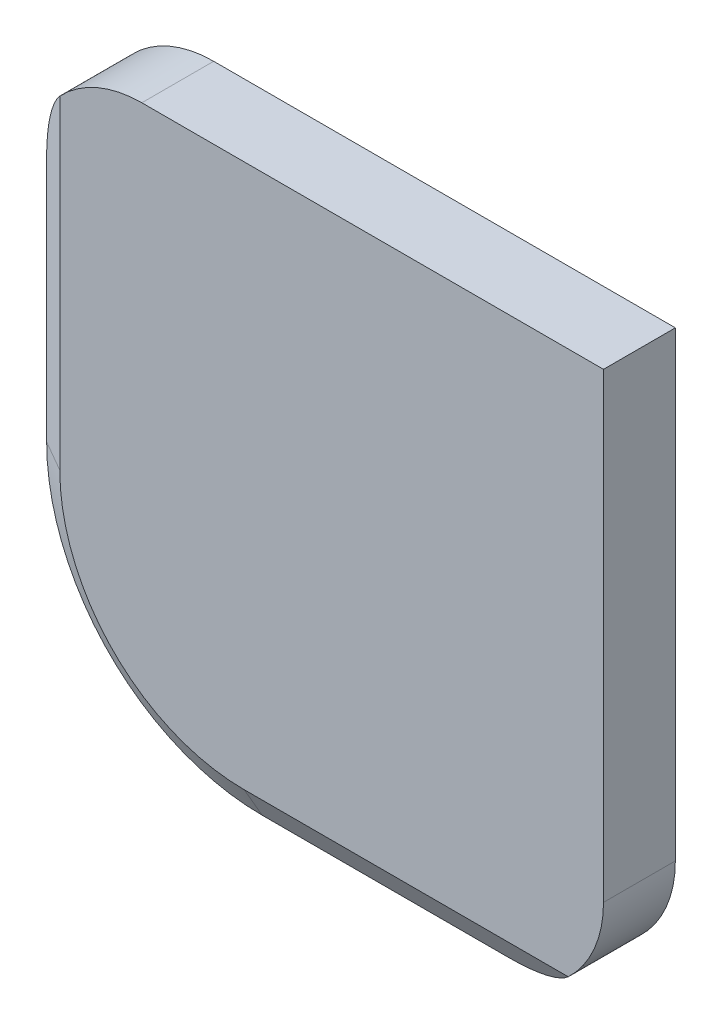
SolidWorks part; units mm, degrees
ref_plane "Front Plane" through (0, 0, 0) normal (0, 0, 1) x (1, 0, 0)
ref_plane "Top Plane" through (0, 0, 0) normal (0, 1, 0) x (1, 0, 0)
ref_plane "Right Plane" through (0, 0, 0) normal (1, 0, 0) x (0, 0, -1)
sketch "Sketch1" plane through (0, 0, 0) normal (0, 0, 1) x (1, 0, 0)
  line L0 (-19.05, 0) -> (-19.05, 31.75)
  line L3 (-19.05, 31.75) -> (31.75, 31.75)
  line L4 (31.75, 31.75) -> (31.75, -19.05)
  line L5 (31.75, -19.05) -> (0, -19.05)
  arc A0 (-19.05, 0) -> (0, -19.05) centre (0, 0) ccw
  dimension "D1" = 50.8
  dimension "D3" = 19.05
  dimension "D2" = 50.8
extrude "Boss-Extrude1" add sketch "Sketch1" along normal blind 6.35
chamfer "Chamfer1" distance 1.5875 angle 60 3 edges at (15.875, -19.05, 6.35) (-13.4704, -13.4704, 6.35) (-19.05, 15.875, 6.35)
chamfer "Chamfer2" distance 2.7432 angle 30 3 edges at (15.875, -19.05, 0) (-13.4704, -13.4704, 0) (-19.05, 15.875, 0)
fillet "Fillet1" radius 10 2 edges at (31.75, -19.05, 3.1731) (-19.05, 31.75, 3.1731)
